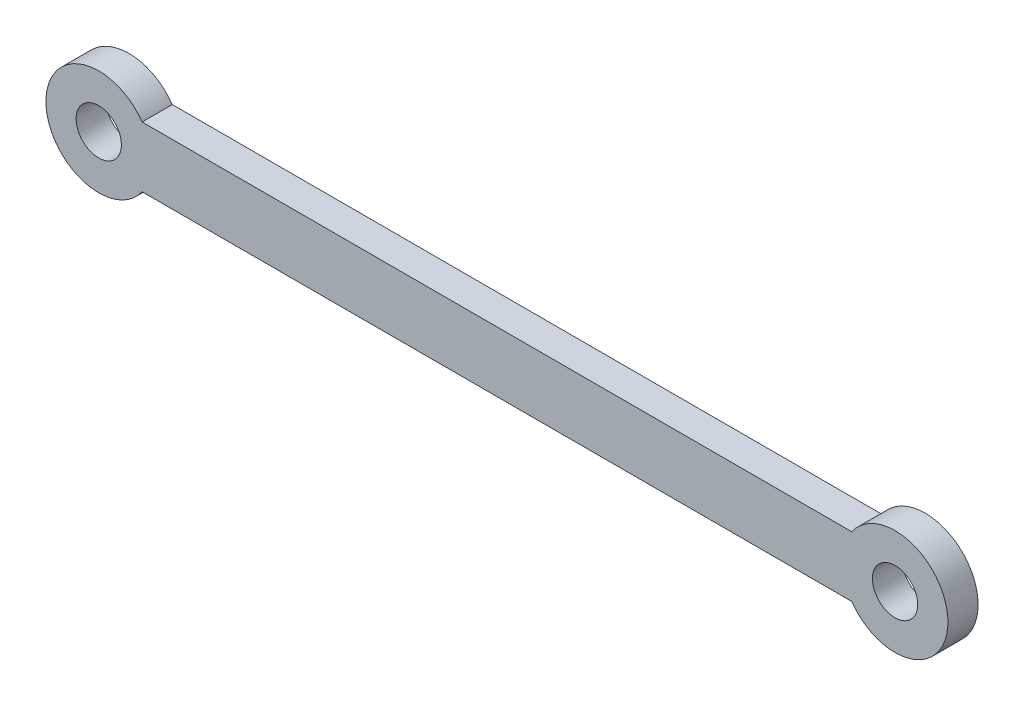
SolidWorks part; units mm, degrees
ref_plane "Alzado" through (0, 0, 0) normal (0, 0, 1) x (1, 0, 0)
ref_plane "Planta" through (0, 0, 0) normal (0, 1, 0) x (1, 0, 0)
ref_plane "Vista lateral" through (0, 0, 0) normal (1, 0, 0) x (0, 0, -1)
sketch "Croquis1" plane through (0, 0, 0) normal (0, 0, 1) x (1, 0, 0)
  line L0 (0, 0) -> (0, 50000) construction
  line L1 (0, 0) -> (50000, 0) construction
  line L2 (-23.5, -2) -> (23.5, -2)
  line L3 (-23.5, -2) -> (-23.5, 2)
  line L4 (-23.5, 2) -> (23.5, 2)
  line L5 (23.5, -2) -> (23.5, 2)
  line L6 (-23.5, -2) -> (23.5, 2) construction
  line L7 (-23.5, 2) -> (23.5, -2) construction
  circle A0 centre (-26.3723, 0) radius 3.5
  circle A1 centre (-26.3723, 0) radius 1.5
  circle A4 centre (26.3723, 0) radius 1.5
  circle A5 centre (26.3723, 0) radius 3.5
  point P5 (0, 0)
  dimension "D2" = 3
  dimension "D5" = 47
  dimension "D6" = 2
  dimension "D1" = 4
extrude "Saliente-Extruir1" add sketch "Croquis1" along normal blind 2 contours L2 A5 L4 A0 | L3 A0 A1 | A5 L5 A4 | L3 A0 | A5 L5
